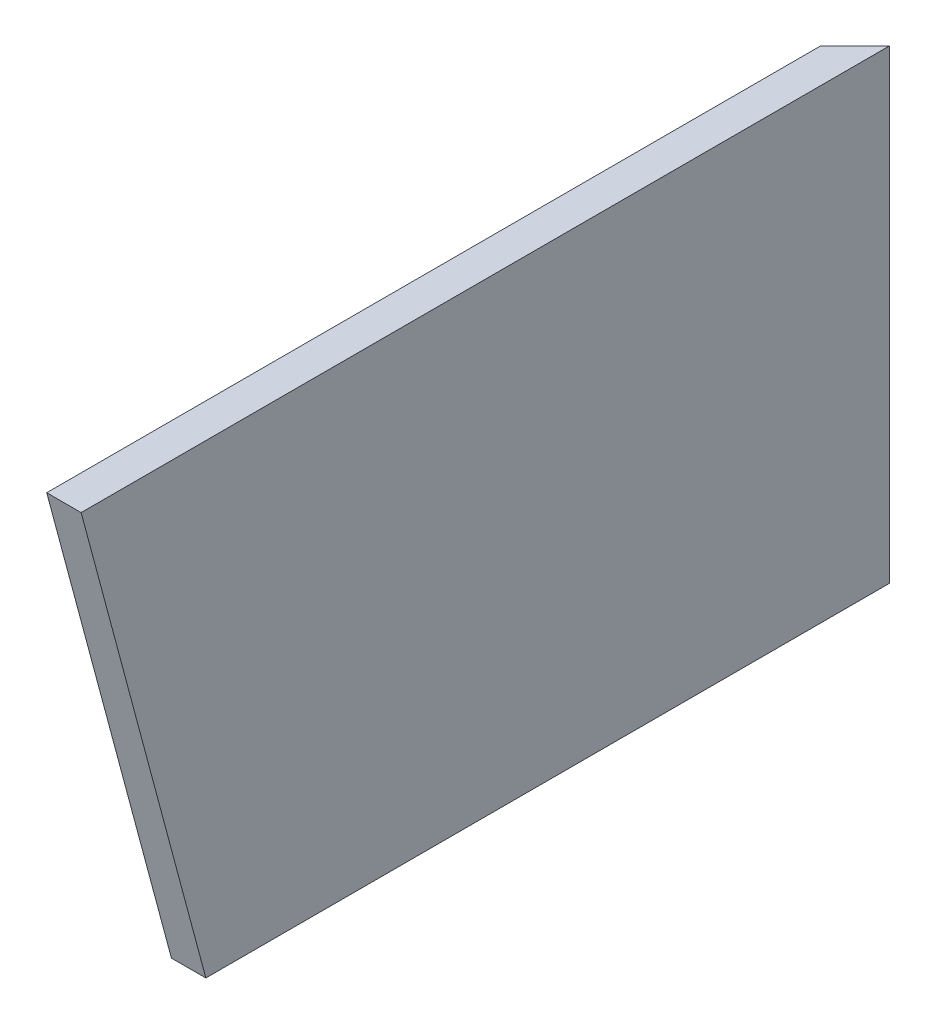
SolidWorks part; units mm, degrees
material "Cedar"
ref_plane "Front Plane" through (0, 0, 0) normal (0, 0, 1) x (1, 0, 0)
ref_plane "Top Plane" through (0, 0, 0) normal (0, 1, 0) x (1, 0, 0)
ref_plane "Right Plane" through (0, 0, 0) normal (1, 0, 0) x (0, 0, -1)
ref_plane "Plane1" through (0, 0, 0) normal (0.7071, 0, 0.7071) x (0.7071, 0, -0.7071)
sketch "Sketch2" plane through (0, 0, 0) normal (0, 0, 1) x (1, 0, 0)
  line L0 (-12.7, 0) -> (0, 0)
  line L1 (0, 0) -> (0, 171.7294)
  line L2 (0, 171.7294) -> (-12.7, 171.7294)
  line L3 (-12.7, 171.7294) -> (-12.7, 0)
  line L4 (0, 0) -> (-12.7, 0) construction
  line L5 (-12.7, 0) -> (-12.7, 177.6975) construction
  dimension "D1" = 0
  dimension "D2" = 12.7
  dimension "D3" = 171.7294
  dimension "D4" = 0
  dimension "D5" = 171.7294
extrude "Boss-Extrude2" add sketch "Sketch2" along normal blind 381
sketch "Sketch3" plane through (0, 0, 0) normal (1, 0, 0) x (0, 0, -1)
  line L0 (-252.1712, 0) -> (-298.186, 171.7294)
  line L1 (55, 0) -> (-55, 0) construction
  line L2 (-381, 171.7294) -> (0, 171.7294) construction
  line L3 (-298.186, 171.7294) -> (-381, 171.7294)
  line L4 (-381, 171.7294) -> (-381, 0)
  line L5 (-381, 0) -> (-252.1712, 0)
  line L6 (0, 55) -> (0, -55) construction
  line L7 (-252.1712, 0) -> (-252.1712, 171.7294) construction
  dimension "D1" = 252.1712
  dimension "D2" = 15
extrude "Cut-Extrude1" cut sketch "Sketch3" against normal through all
mirror "Mirror2" [suppressed] about plane through (0, 0, 0) normal (0.7071, 0, 0.7071)
sketch "Sketch4" plane through (0, 171.7294, 0) normal (0, 1, 0) x (1, 0, 0)
  line L0 (0, 0) -> (-12.7, -12.7)
  line L1 (-12.7, -298.186) -> (-12.7, 0) construction
  line L2 (-12.7, -12.7) -> (-12.7, 0)
  line L3 (0, 0) -> (-12.7, 0) construction
  line L4 (-12.7, 0) -> (0, 0)
  dimension "D1" = 45
extrude "Cut-Extrude2" cut sketch "Sketch4" against normal through all
